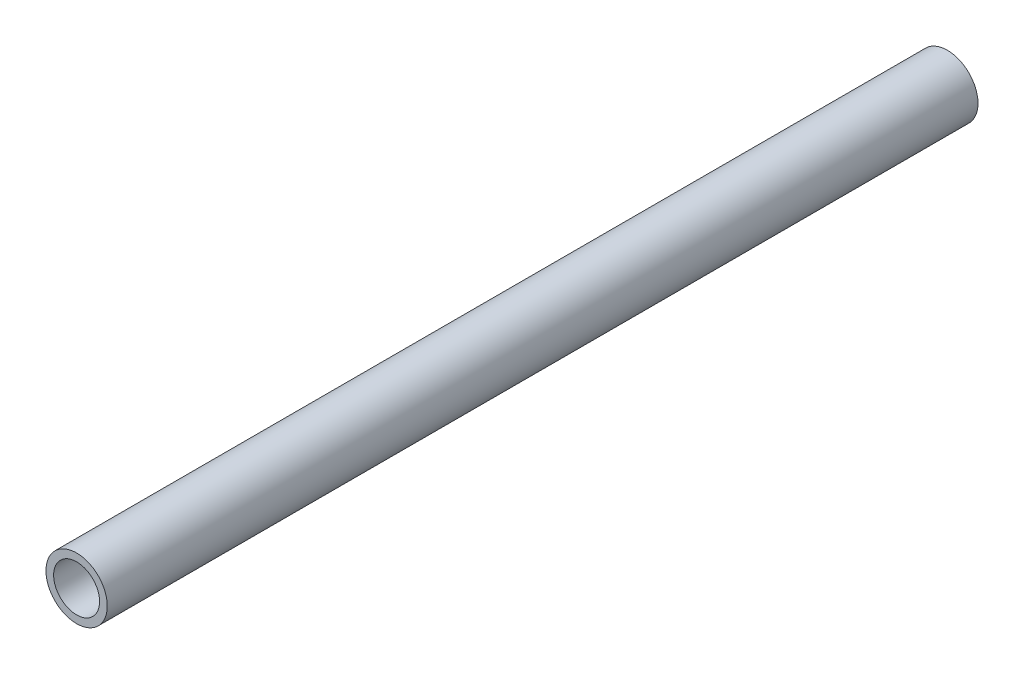
SolidWorks part; units mm, degrees
material "6061-T6 (SS)"
ref_plane "Front Plane" through (0, 0, 0) normal (0, 0, 1) x (1, 0, 0)
ref_plane "Top Plane" through (0, 0, 0) normal (0, 1, 0) x (1, 0, 0)
ref_plane "Right Plane" through (0, 0, 0) normal (1, 0, 0) x (0, 0, -1)
sketch "Sketch1" plane through (0, 0, 0) normal (0, 0, 1) x (1, 0, 0)
  circle A0 centre (0, 0) radius 6.35
  circle A1 centre (0, 0) radius 4.7625
  dimension "D1" = 12.7
  dimension "D2" = 9.525
extrude "Boss-Extrude1" add sketch "Sketch1" along normal blind 180.3667
